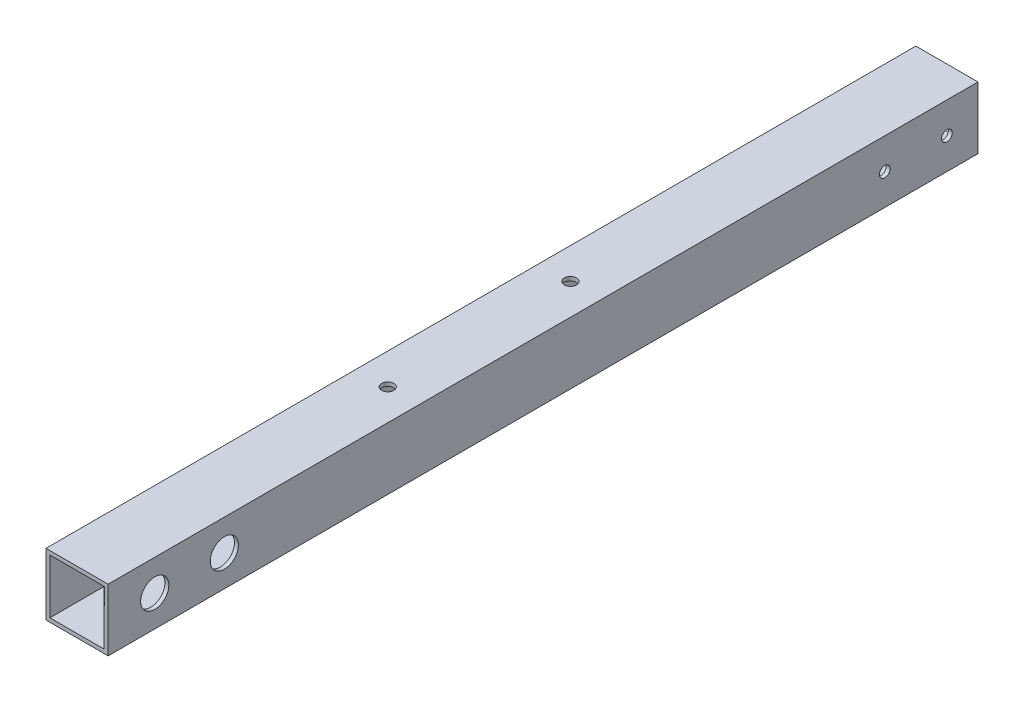
SolidWorks part; units mm, degrees
material "Acrylic (Medium-high impact)"
ref_plane "Front Plane" through (0, 0, 0) normal (0, 0, 1) x (1, 0, 0)
ref_plane "Top Plane" through (0, 0, 0) normal (0, 1, 0) x (1, 0, 0)
ref_plane "Right Plane" through (0, 0, 0) normal (1, 0, 0) x (0, 0, -1)
sketch "Sketch1" plane through (0, 0, 0) normal (0, 0, 1) x (1, 0, 0)
  line L1 (-12.7, 12.7) -> (12.7, 12.7)
  line L2 (-12.7, 12.7) -> (-12.7, -12.7)
  line L3 (-12.7, -12.7) -> (12.7, -12.7)
  line L4 (12.7, 12.7) -> (12.7, -12.7)
  line L5 (-12.7, 12.7) -> (12.7, -12.7) construction
  line L6 (-12.7, -12.7) -> (12.7, 12.7) construction
  line L7 (-11.1125, 11.1125) -> (11.1125, 11.1125)
  line L8 (-11.1125, 11.1125) -> (-11.1125, -11.1125)
  line L9 (-11.1125, -11.1125) -> (11.1125, -11.1125)
  line L10 (11.1125, 11.1125) -> (11.1125, -11.1125)
  line L11 (-11.1125, 11.1125) -> (11.1125, -11.1125) construction
  line L12 (-11.1125, -11.1125) -> (11.1125, 11.1125) construction
  point P0 (0, 0)
  point P6 (0, 0)
  dimension "D1" = 25.4
  dimension "D2" = 25.4
  dimension "D3" = 22.225
extrude "Boss-Extrude1" add sketch "Sketch1" along normal blind 355.6
sketch "Sketch5" plane through (-12.7, 0, 0) normal (-1, 0, 0) x (0, 0, 1)
  line L1 (355.6, -12.7) -> (355.6, 12.7) construction
  line L2 (355.6, -12.7) -> (0, -12.7) construction
  line L3 (355.6, 12.7) -> (0, 12.7) construction
  line L4 (336.55, 12.7) -> (336.55, -12.7) construction
  circle A4 centre (336.55, 0) radius 2.4892
  circle A5 centre (308.102, 0) radius 2.4892
  dimension "D1" = 4.9784
  dimension "D2" = 28.448
  dimension "D3" = 19.05
extrude "Cut-Extrude2" cut sketch "Sketch5" against normal blind 2.54
sketch "Sketch6" plane through (0, -12.7, 0) normal (0, -1, 0) x (1, 0, 0)
  line L0 (-12.7, 228.6) -> (12.7, 228.6) construction
  line L1 (-12.7, 355.6) -> (-12.7, 0) construction
  line L2 (12.7, 355.6) -> (12.7, 0) construction
  line L3 (-12.7, 355.6) -> (12.7, 355.6) construction
  circle A0 centre (0, 228.6) radius 5.715
  circle A1 centre (0, 153.924) radius 5.715
  dimension "D1" = 11.43
  dimension "D2" = 74.676
  dimension "D3" = 127
extrude "Cut-Extrude3" cut sketch "Sketch6" against normal blind 6.35
sketch "Sketch7" plane through (0, 12.7, 0) normal (0, 1, 0) x (1, 0, 0)
  line L0 (12.7, -355.6) -> (-12.7, -355.6) construction
  line L4 (12.7, -228.6) -> (-12.7, -228.6) construction
  line L5 (12.7, -355.6) -> (12.7, 0) construction
  line L6 (-12.7, -355.6) -> (-12.7, 0) construction
  circle A0 centre (0, -228.6) radius 2.4892
  circle A1 centre (0, -153.924) radius 2.4892
  dimension "D3" = 4.9784
  dimension "D1" = 127
  dimension "D2" = 74.676
extrude "Cut-Extrude4" cut sketch "Sketch7" against normal blind 2.54
sketch "Sketch8" plane through (12.7, 0, 0) normal (1, 0, 0) x (0, 0, -1)
  line L0 (-355.6, -12.7) -> (-355.6, 12.7) construction
  line L1 (-308.102, -12.7) -> (-308.102, 12.7) construction
  line L2 (-355.6, -12.7) -> (0, -12.7) construction
  line L3 (-355.6, 12.7) -> (0, 12.7) construction
  circle A0 centre (-336.55, 0) radius 5.7544
  circle A1 centre (-308.102, 0) radius 5.7544
  dimension "D1" = 11.5087
  dimension "D2" = 19.05
  dimension "D3" = 28.448
extrude "Cut-Extrude5" cut sketch "Sketch8" against normal blind 2.54
sketch "Sketch10" plane through (-12.7, 0, 0) normal (-1, 0, 0) x (0, 0, 1)
  line L0 (0, 12.7) -> (0, -12.7) construction
  circle A0 centre (12.7, 0) radius 2.1828
  circle A1 centre (38.1, 0) radius 2.1828
  point P6 (0, 0)
  dimension "D1" = 4.3656
  dimension "D3" = 12.7
  dimension "D4" = 25.4
extrude "Cut-Extrude7" cut sketch "Sketch10" against normal up to surface (25.4 mm away) up to face at (12.7, 5.7544, 336.55)
